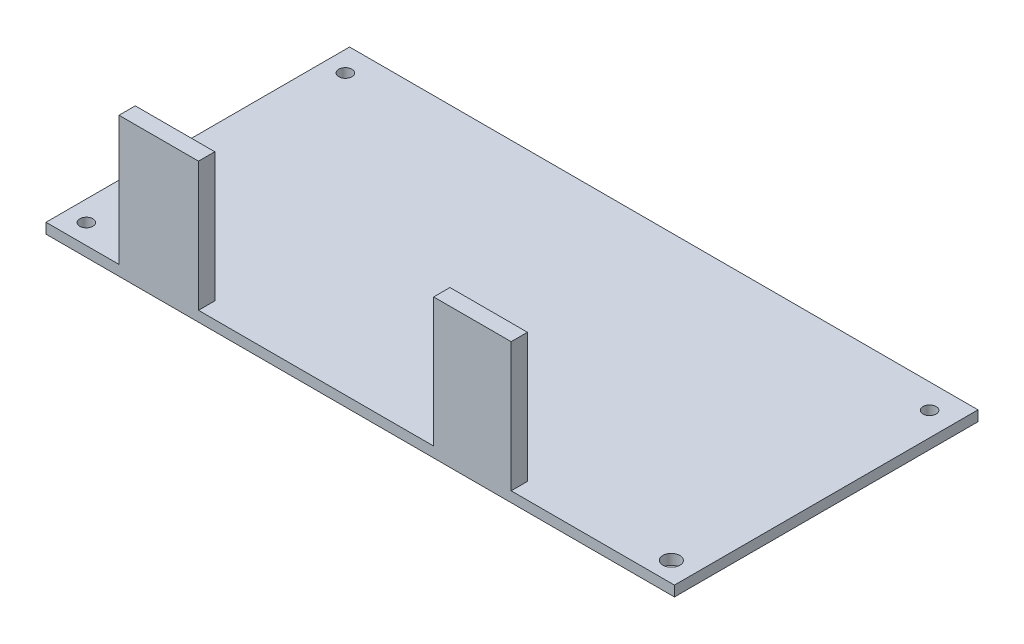
SolidWorks part; units mm, degrees
ref_plane "Front" through (0, 0, 0) normal (0, 0, 1) x (1, 0, 0)
ref_plane "Top" through (0, 0, 0) normal (0, 1, 0) x (1, 0, 0)
ref_plane "Right" through (0, 0, 0) normal (1, 0, 0) x (0, 0, -1)
sketch "Sketch1" plane through (0, 0, 0) normal (0, 1, 0) x (1, 0, 0)
  line L1 (0, 0) -> (97.3, 0)
  line L2 (0, 0) -> (0, -47)
  line L3 (0, -47) -> (97.3, -47)
  line L4 (97.3, 0) -> (97.3, -47)
  dimension "D1" = 97.3
  dimension "D2" = 47
extrude "Boss-Extrude1" add sketch "Sketch1" along normal blind 1.6
sketch "Sketch2" plane through (0, 1.6, 0) normal (0, 1, 0) x (1, 0, 0)
  line L0 (0, -47) -> (97.3, -47) construction
  line L1 (11.3007, -47) -> (23.6115, -47)
  line L2 (11.3007, -47) -> (11.3007, -44.4786)
  line L3 (11.3007, -44.4786) -> (23.6115, -44.4786)
  line L4 (23.6115, -47) -> (23.6115, -44.4786)
  line L6 (60.0201, -47) -> (72.018, -47)
  line L7 (60.0201, -47) -> (60.0201, -44.4786)
  line L8 (60.0201, -44.4786) -> (72.018, -44.4786)
  line L9 (72.018, -47) -> (72.018, -44.4786)
extrude "Boss-Extrude2" add sketch "Sketch2" along normal blind 20
sketch "Sketch3" plane through (0, 1.6, 0) normal (0, 1, 0) x (1, 0, 0)
  line L0 (0, 0) -> (0, -47) construction
  line L1 (97.3, 0) -> (0, 0) construction
  line L2 (97.3, -47) -> (97.3, 0) construction
  line L3 (0, -47) -> (11.3007, -47) construction
  line L4 (72.018, -47) -> (97.3, -47) construction
  circle A0 centre (3.16, -3.81) radius 1.016
  circle A1 centre (93.617, -3.81) radius 1.016
  circle A2 centre (93.744, -43.916) radius 1.316
  circle A3 centre (3.16, -43.916) radius 1.016
  point P10 (0, 0)
  dimension "D1" = 2.032
  dimension "D2" = 2.032
  dimension "D3" = 2.032
  dimension "D4" = 2.632
  dimension "D5" = 3.16
  dimension "D6" = 3.81
  dimension "D7" = 3.683
  dimension "D8" = 3.81
  dimension "D9" = 3.16
  dimension "D10" = 3.084
  dimension "D11" = 3.556
  dimension "D12" = 3.084
extrude "Cut-Extrude3" cut sketch "Sketch3" against normal through all
